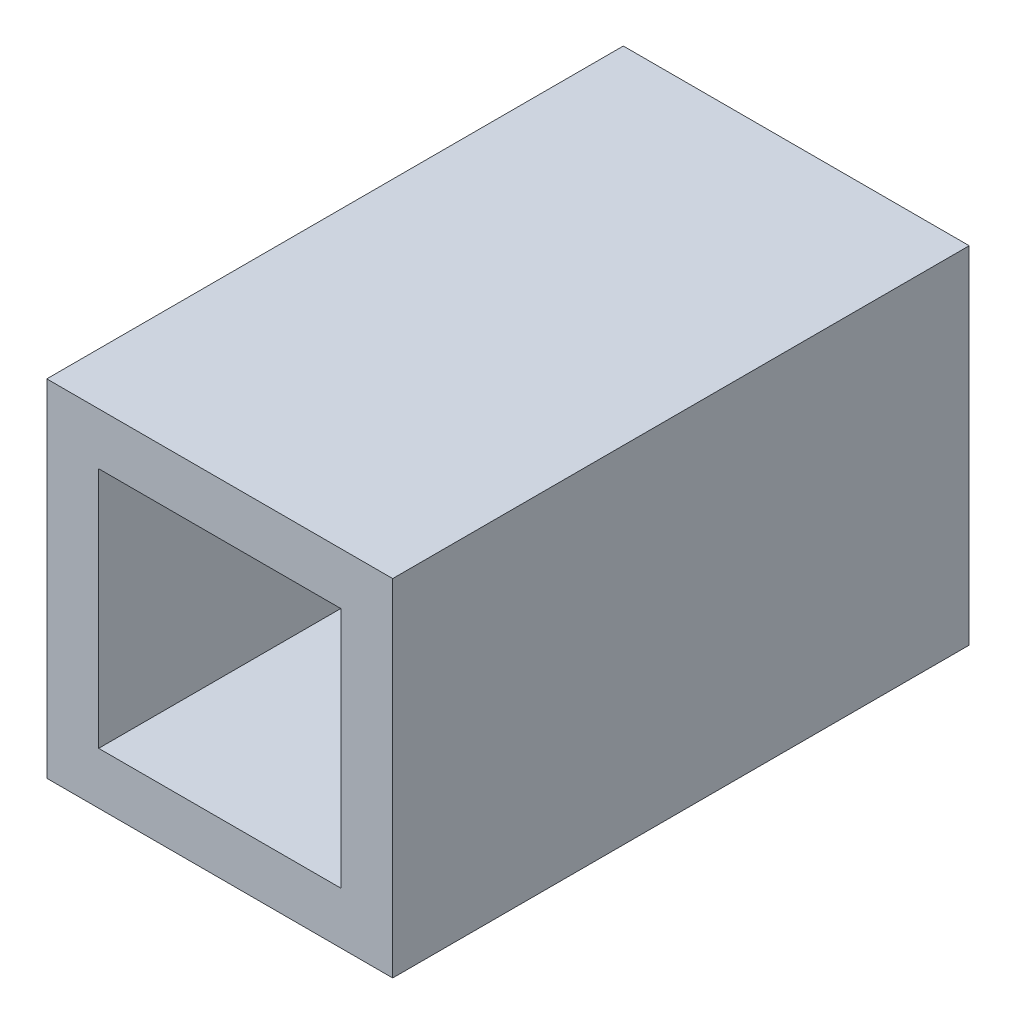
SolidWorks part; units mm, degrees
material "ABS"
ref_plane "Front Plane" through (0, 0, 0) normal (0, 0, 1) x (1, 0, 0)
ref_plane "Top Plane" through (0, 0, 0) normal (0, 1, 0) x (1, 0, 0)
ref_plane "Right Plane" through (0, 0, 0) normal (1, 0, 0) x (0, 0, -1)
sketch "Sketch1" plane through (0, 0, 0) normal (0, 0, 1) x (1, 0, 0)
  line L1 (0, 0) -> (4.2, 0)
  line L2 (0, 0) -> (0, 4.2)
  line L3 (0, 4.2) -> (4.2, 4.2)
  line L4 (4.2, 0) -> (4.2, 4.2)
  line L5 (5.1, 5.1) -> (-0.9, 5.1)
  line L6 (5.1, 5.1) -> (5.1, -0.9)
  line L7 (5.1, -0.9) -> (-0.9, -0.9)
  line L8 (-0.9, 5.1) -> (-0.9, -0.9)
  point P9 (2.1, 4.2)
  point P10 (2.1, 5.1)
  point P11 (4.2, 2.1)
  point P12 (5.1, 2.1)
  dimension "D1" = 6
  dimension "D2" = 6
  dimension "D3" = 4.2
  dimension "D4" = 4.2
extrude "Boss-Extrude1" add sketch "Sketch1" along normal blind 10
